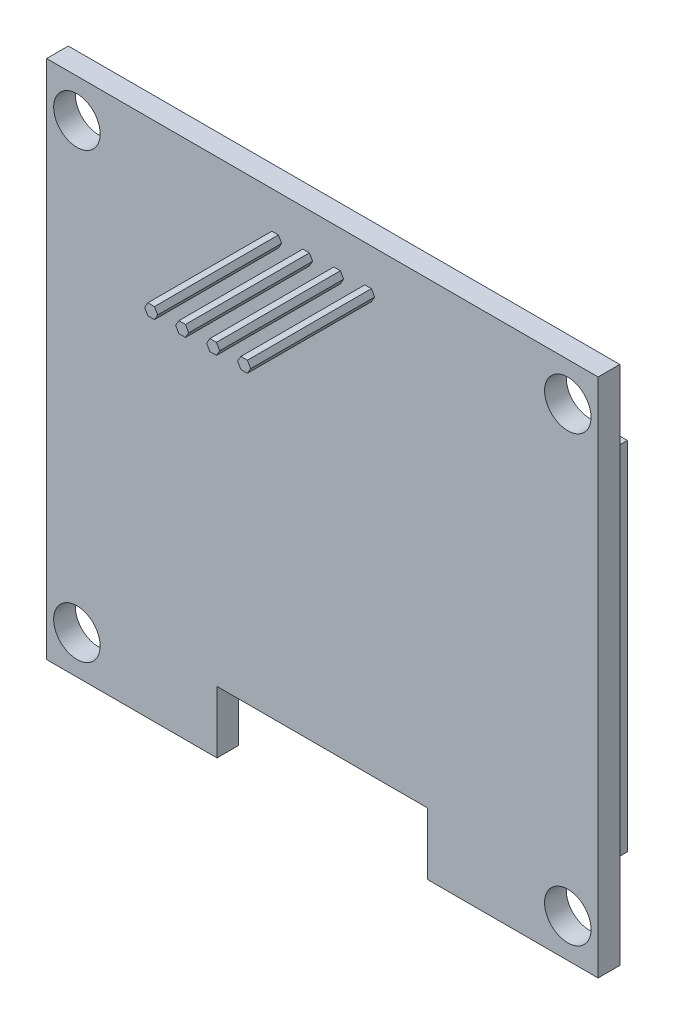
SolidWorks part; units mm, degrees
ref_plane "Front Plane" through (0, 0, 0) normal (0, 0, 1) x (1, 0, 0)
ref_plane "Top Plane" through (0, 0, 0) normal (0, 1, 0) x (1, 0, 0)
ref_plane "Right Plane" through (0, 0, 0) normal (1, 0, 0) x (0, 0, -1)
sketch "Sketch1" plane through (0, 0, 0) normal (0, 0, 1) x (1, 0, 0)
  line L0 (0, -55) -> (0, 55) construction
  line L1 (-17.8, 16.8) -> (17.8, 16.8)
  line L2 (-17.8, 16.8) -> (-17.8, -16.8)
  line L3 (-17.8, -16.8) -> (17.8, -16.8)
  line L4 (17.8, 16.8) -> (17.8, -16.8)
  line L5 (-17.8, 16.8) -> (17.8, -16.8) construction
  line L6 (-17.8, -16.8) -> (17.8, 16.8) construction
  line L7 (-6.8, -20.8) -> (6.8, -20.8)
  line L8 (-6.8, -20.8) -> (-6.8, -12.8)
  line L9 (-6.8, -12.8) -> (6.8, -12.8)
  line L10 (6.8, -20.8) -> (6.8, -12.8)
  line L11 (-6.8, -20.8) -> (6.8, -12.8) construction
  line L12 (-6.8, -12.8) -> (6.8, -20.8) construction
  line L14 (55, 0) -> (-55, 0) construction
  circle A0 centre (-15.8437, 14.3136) radius 1.5
  circle A1 centre (15.8437, 14.3136) radius 1.5
  circle A2 centre (15.8437, -14.3136) radius 1.5
  circle A3 centre (-15.8437, -14.3136) radius 1.5
  point P0 (0, 0)
  point P6 (0, -16.8)
  point P13 (-15.8437, 14.3136)
  point P24 (0, 0)
  dimension "D1" = 35.6
  dimension "D2" = 33.6
  dimension "D3" = 8
  dimension "D4" = 11
extrude "Boss-Extrude1" add sketch "Sketch1" along normal blind 1.4 contours L10 L3 L4 L1 L2 L8 L9 A1 A0 A2 A3
sketch "Sketch2" plane through (0, 0, 0) normal (0, 0, -1) x (-1, 0, 0)
  line L1 (-16.9912, 11.5) -> (16.9912, 11.5)
  line L2 (-16.9912, 11.5) -> (-16.9912, -11.5)
  line L3 (-16.9912, -11.5) -> (16.9912, -11.5)
  line L4 (16.9912, 11.5) -> (16.9912, -11.5)
  line L5 (-16.9912, 11.5) -> (16.9912, -11.5) construction
  line L6 (-16.9912, -11.5) -> (16.9912, 11.5) construction
  point P0 (0, 0)
  dimension "D1" = 23
extrude "Boss-Extrude2" add sketch "Sketch2" along normal blind 1.3
sketch "Sketch3" plane through (0, 0, 1.4) normal (0, 0, 1) x (1, 0, 0)
  line L0 (-0.6257, 14.0514) -> (-0.8369, 14.4173)
  line L1 (-2.6257, 14.0514) -> (-2.8369, 14.4173)
  line L2 (-2.8369, 14.4173) -> (-3.2594, 14.4173)
  line L3 (-3.2594, 14.4173) -> (-3.4707, 14.0514)
  line L4 (-3.4707, 14.0514) -> (-3.2594, 13.6855)
  line L5 (-3.2594, 13.6855) -> (-2.8369, 13.6855)
  line L6 (-2.8369, 13.6855) -> (-2.6257, 14.0514)
  line L7 (-0.8369, 14.4173) -> (-1.2594, 14.4173)
  line L8 (-1.2594, 14.4173) -> (-1.4707, 14.0514)
  line L9 (-1.4707, 14.0514) -> (-1.2594, 13.6855)
  line L10 (-1.2594, 13.6855) -> (-0.8369, 13.6855)
  line L11 (-0.8369, 13.6855) -> (-0.6257, 14.0514)
  line L12 (1.3743, 14.0514) -> (1.1631, 14.4173)
  line L13 (1.1631, 14.4173) -> (0.7406, 14.4173)
  line L14 (0.7406, 14.4173) -> (0.5293, 14.0514)
  line L15 (0.5293, 14.0514) -> (0.7406, 13.6855)
  line L16 (0.7406, 13.6855) -> (1.1631, 13.6855)
  line L17 (1.1631, 13.6855) -> (1.3743, 14.0514)
  line L18 (3.3743, 14.0514) -> (3.1631, 14.4173)
  line L19 (3.1631, 14.4173) -> (2.7406, 14.4173)
  line L20 (2.7406, 14.4173) -> (2.5293, 14.0514)
  line L21 (2.5293, 14.0514) -> (2.7406, 13.6855)
  line L22 (2.7406, 13.6855) -> (3.1631, 13.6855)
  line L23 (3.1631, 13.6855) -> (3.3743, 14.0514)
  circle A0 centre (-3.0482, 14.0514) radius 0.3659 construction
  circle A1 centre (-1.0482, 14.0514) radius 0.3659 construction
  circle A2 centre (0.9518, 14.0514) radius 0.3659 construction
  circle A3 centre (2.9518, 14.0514) radius 0.3659 construction
  point P1 (2.9518, 14.0514)
  dimension "D1" = 4
extrude "Boss-Extrude3" add sketch "Sketch3" along normal blind 8
